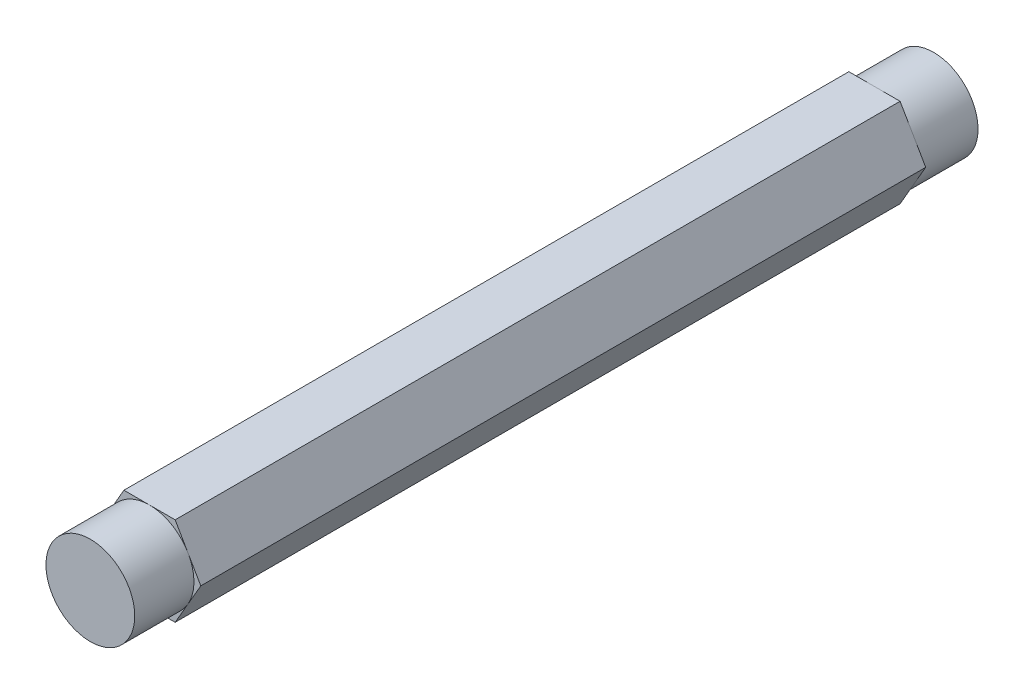
SolidWorks part; units mm, degrees
material "6061-T6 (SS)"
ref_plane "Front Plane" through (0, 0, 0) normal (0, 0, 1) x (1, 0, 0)
ref_plane "Top Plane" through (0, 0, 0) normal (0, 1, 0) x (1, 0, 0)
ref_plane "Right Plane" through (0, 0, 0) normal (1, 0, 0) x (0, 0, -1)
sketch "Sketch1" plane through (0, 0, 0) normal (0, 0, 1) x (1, 0, 0)
  line L1 (-2.7496, -4.7625) -> (2.7496, -4.7625)
  line L2 (2.7496, -4.7625) -> (5.4993, 0)
  line L3 (5.4993, 0) -> (2.7496, 4.7625)
  line L4 (2.7496, 4.7625) -> (-2.7496, 4.7625)
  line L5 (-2.7496, 4.7625) -> (-5.4993, 0)
  line L6 (-5.4993, 0) -> (-2.7496, -4.7625)
  circle A0 centre (0, 0) radius 4.7625 construction
  dimension "D1" = 9.525
extrude "Boss-Extrude1" add sketch "Sketch1" along normal blind 77.7875
sketch "Sketch2" plane through (0, 0, 77.7875) normal (0, 0, 1) x (1, 0, 0)
  circle A0 centre (0, 0) radius 4.7625
  dimension "D1" = 9.525
extrude "Boss-Extrude2" add sketch "Sketch2" along normal blind 6.35
sketch "Sketch3" plane through (0, 0, 0) normal (0, 0, -1) x (-1, 0, 0)
  circle A0 centre (0, 0) radius 4.7625
  dimension "D1" = 9.525
extrude "Boss-Extrude3" add sketch "Sketch3" along normal blind 6.35
